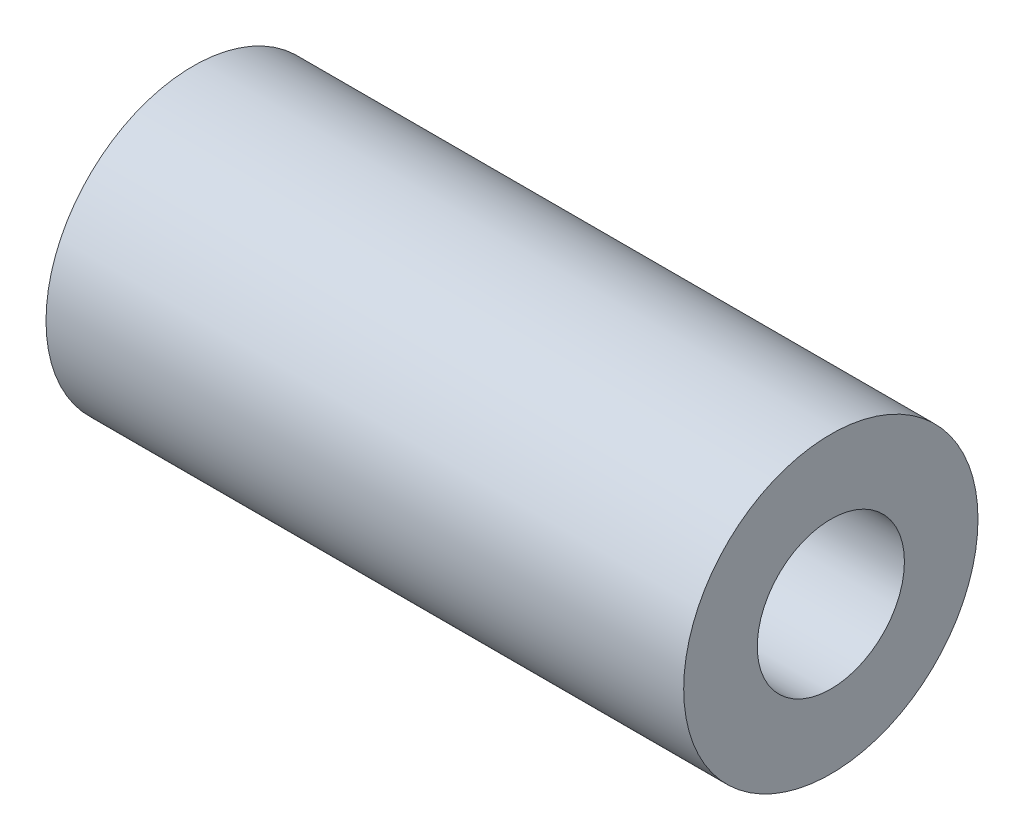
SolidWorks part; units mm, degrees
ref_plane "前视基准面" through (0, 0, 0) normal (0, 0, 1) x (1, 0, 0)
ref_plane "上视基准面" through (0, 0, 0) normal (0, 1, 0) x (1, 0, 0)
ref_plane "右视基准面" through (0, 0, 0) normal (1, 0, 0) x (0, 0, -1)
sketch "草图1" plane through (0, 0, 0) normal (1, 0, 0) x (0, 0, -1)
  circle A0 centre (0, 0) radius 1.5
  circle A1 centre (0, 0) radius 3
  dimension "D1" = 3
  dimension "D2" = 6
extrude "凸台-拉伸1" add sketch "草图1" along normal blind 13
